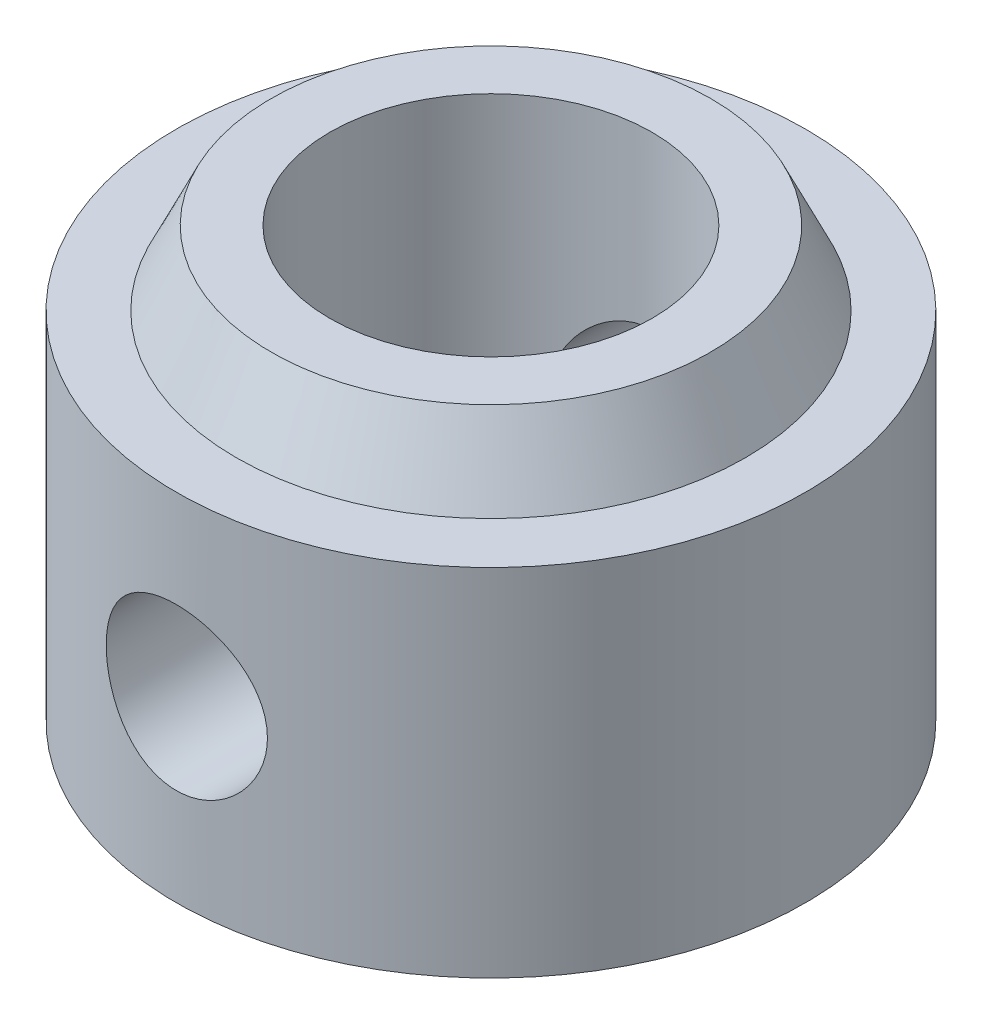
SolidWorks part; units mm, degrees
ref_plane "Front Plane" through (0, 0, 0) normal (0, 0, 1) x (1, 0, 0)
ref_plane "Top Plane" through (0, 0, 0) normal (0, 1, 0) x (1, 0, 0)
ref_plane "Right Plane" through (0, 0, 0) normal (1, 0, 0) x (0, 0, -1)
sketch "Sketch2" plane through (0, 0, 0) normal (0, 0, 1) x (1, 0, 0)
  line L0 (0, 0) -> (0, 6.1232) construction
  line L1 (2.05, 5.461) -> (2.05, 0)
  line L2 (2.05, 0) -> (4.0005, 0)
  line L3 (4.0005, 0) -> (4.0005, 4.5212)
  line L5 (4.0005, 4.5212) -> (3.2385, 4.5212)
  line L6 (2.794, 5.461) -> (2.05, 5.461)
  line L7 (3.2385, 4.5212) -> (2.794, 5.461)
  point P7 (0, 0)
  point P8 (3.2952, 5.0953)
  point P10 (2, 2.5804)
  point P11 (3.2501, 2.0834)
  point P12 (3.461, 5.461)
  point P13 (2.6778, 5.461)
  point P14 (4.0005, 5.461)
  point P15 (2.256, 5.461)
  point P16 (3.2802, 5.461)
  point P17 (0, 0)
  point P18 (4.0005, 5.461)
  point P19 (4.0005, 4.8472)
  point P20 (3.6041, 5.461)
  point P21 (4.0005, 4.802)
  dimension "D1" = 4.1
  dimension "D2" = 8.001
  dimension "D3" = 5.461
  dimension "D4" = 4.5212
  dimension "D5" = 6.477
  dimension "D6" = 5.588
revolve "Revolve1" add sketch "Sketch2" angle 360 about L0
hole_wizard "M2.5x0.45 Tapped Hole1" positions "3DSketch1" profile "Sketch3" tap size "M2.5x0.45" standard "ANSI Metric" end condition through all
sketch3d "3DSketch1"
  line L0 (0, 4.5212, 4.0005) -> (0, 0, 4.0005) construction
  line L3 (0, 2.2606, 4.0005) -> (0, 2.2606, 0) construction
  line L5 (0, 2.2606, 0) -> (0, 0, 0) construction
  circle A0 centre (0, 4.5212, 0) radius 4.0005 construction
  circle A1 centre (0, 0, 0) radius 4.0005 construction
  point P0 (0, 2.2606, 4.0005)
  point P7 (0, 0.5207, 0)
  point P10 (0, -4.0005, 0)
sketch "Sketch3" plane through (0, 2.2606, 4.0005) normal (1, 0, 0) x (0, -1, 0)
  line L0 (0, 0) -> (0, 8.001)
  line L1 (0, 8.001) -> (1.025, 8.001)
  line L2 (1.025, 8.001) -> (1.025, 0)
  line L5 (1.025, 0) -> (0, 0)
  line L11 (0, -6.35) -> (0, 107.95) construction
  dimension "Thru Tap Drill Dia." = 2.05
  dimension "Thru Tap Drill Depth" = 8.001
cosmetic thread "Hole Thread1"
